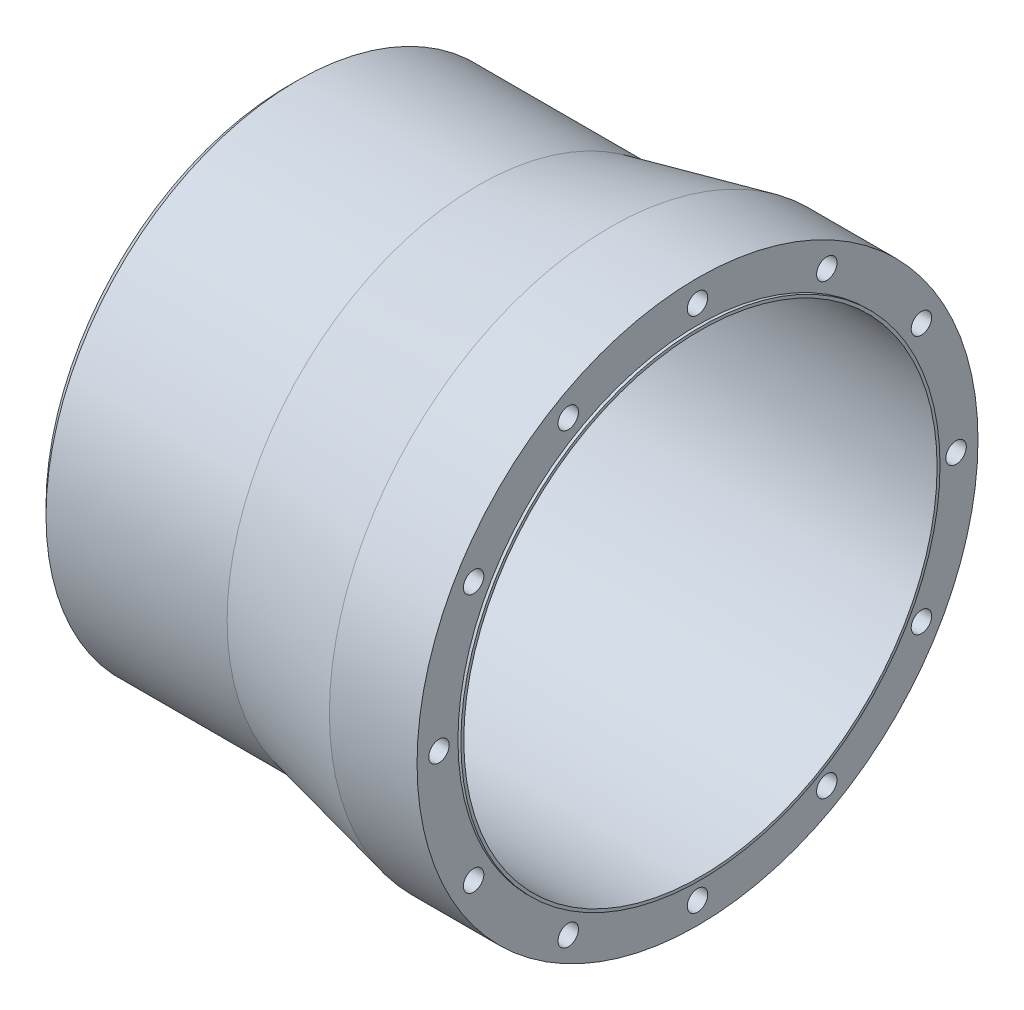
SolidWorks part; units mm, degrees
material "AISI 316 不锈钢板 (SS)"
ref_plane "前视基准面" through (0, 0, 0) normal (0, 0, 1) x (1, 0, 0)
ref_plane "上视基准面" through (0, 0, 0) normal (0, 1, 0) x (1, 0, 0)
ref_plane "右视基准面" through (0, 0, 0) normal (1, 0, 0) x (0, 0, -1)
sketch "草图2" plane through (0, 0, 0) normal (0, 0, 1) x (1, 0, 0)
  line L0 (0, 0) -> (172.3498, 0) construction
  line L2 (10, 81) -> (150, 81)
  line L3 (10, 86) -> (75, 86)
  line L4 (150, 86) -> (150, 81)
  line L5 (150, 86) -> (150, 96)
  line L6 (150, 96) -> (120, 96)
  line L7 (120, 96) -> (75, 86)
  line L8 (10, 81) -> (10, 86)
revolve "旋转1" add sketch "草图2" angle 360 about L0
chamfer "倒角2" distance 3 angle 45 1 edges at (10, 0, 86)
sketch "草图4" plane through (150, 0, 0) normal (1, 0, 0) x (0, 0, -1)
  circle A0 centre (44.25, 76.6432) radius 3.5
  circle A2 centre (0, 88.5) radius 3.5
  circle A3 centre (76.6432, 44.25) radius 3.5
  circle A4 centre (88.5, 0) radius 3.5
  circle A5 centre (76.6432, -44.25) radius 3.5
  circle A6 centre (44.25, -76.6432) radius 3.5
  circle A7 centre (0, -88.5) radius 3.5
  circle A8 centre (-44.25, -76.6432) radius 3.5
  circle A9 centre (-76.6432, -44.25) radius 3.5
  circle A10 centre (-88.5, 0) radius 3.5
  circle A11 centre (-76.6432, 44.25) radius 3.5
  circle A12 centre (-44.25, 76.6432) radius 3.5
  point P29 (0, 0)
  dimension "D1" = 12
extrude "切除-拉伸1" cut sketch "草图4" against normal blind 10
sketch "草图5" plane through (150, 0, 0) normal (1, 0, 0) x (0, 0, -1)
  circle A0 centre (0, 0) radius 81
  circle A1 centre (0, 0) radius 82
extrude "凸台-拉伸1" add sketch "草图5" along normal blind 1
